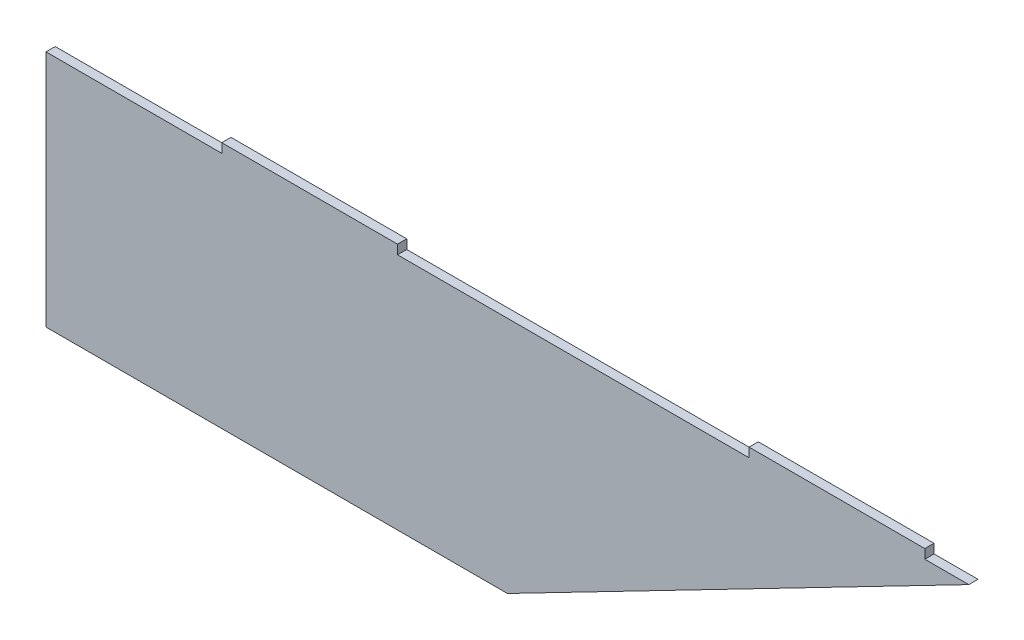
SolidWorks part; units mm, degrees
ref_plane "Plano frontal" through (0, 0, 0) normal (0, 0, 1) x (1, 0, 0)
ref_plane "Plano superior" through (0, 0, 0) normal (0, 1, 0) x (1, 0, 0)
ref_plane "Plano direito" through (0, 0, 0) normal (1, 0, 0) x (0, 0, -1)
sketch "Esboço1" plane through (0, 0, 0) normal (0, 0, 1) x (1, 0, 0)
  line L0 (0, 0) -> (0, 77.5)
  line L1 (0, 77.5) -> (57.1429, 77.5)
  line L2 (300, 77.5) -> (150, 0)
  line L3 (150, 0) -> (0, 0)
  line L4 (57.1429, 77.5) -> (57.1429, 80.5)
  line L5 (57.1429, 80.5) -> (114.2857, 80.5)
  line L6 (114.2857, 80.5) -> (114.2857, 77.5)
  line L7 (228.5714, 77.5) -> (228.5714, 80.5)
  line L8 (228.5714, 80.5) -> (285.7143, 80.5)
  line L9 (285.7143, 80.5) -> (285.7143, 77.5)
  line L10 (114.2857, 77.5) -> (228.5714, 77.5)
  line L11 (285.7143, 77.5) -> (300, 77.5)
  point P11 (0, 0)
  point P14 (0, 0)
  dimension "D1" = 57.1429
  dimension "D2" = 57.1429
  dimension "D3" = 57.1429
  dimension "D4" = 114.2857
  dimension "D5" = 3
  dimension "D6" = 300
  dimension "D7" = 150
  dimension "D8" = 77.5
extrude "Ressalto-extrusão1" add sketch "Esboço1" along normal blind 3
